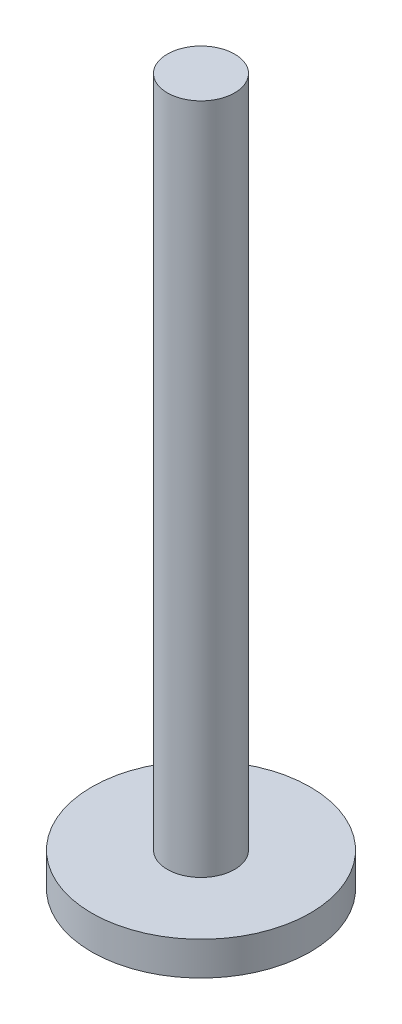
SolidWorks part; units mm, degrees
ref_plane "Front Plane" through (0, 0, 0) normal (0, 0, 1) x (1, 0, 0)
ref_plane "Top Plane" through (0, 0, 0) normal (0, 1, 0) x (1, 0, 0)
ref_plane "Right Plane" through (0, 0, 0) normal (1, 0, 0) x (0, 0, -1)
sketch "Sketch3" plane through (0, 0, 0) normal (0, 1, 0) x (1, 0, 0)
  circle A0 centre (0, 0) radius 41.275
  dimension "D1" = 82.55
extrude "Boss-Extrude3" add sketch "Sketch3" along normal blind 12.7
sketch "Sketch4" plane through (0, 12.7, 0) normal (0, 1, 0) x (1, 0, 0)
  circle A0 centre (0, 0) radius 12.7
extrude "Boss-Extrude4" add sketch "Sketch4" along normal blind 254 contours A0
